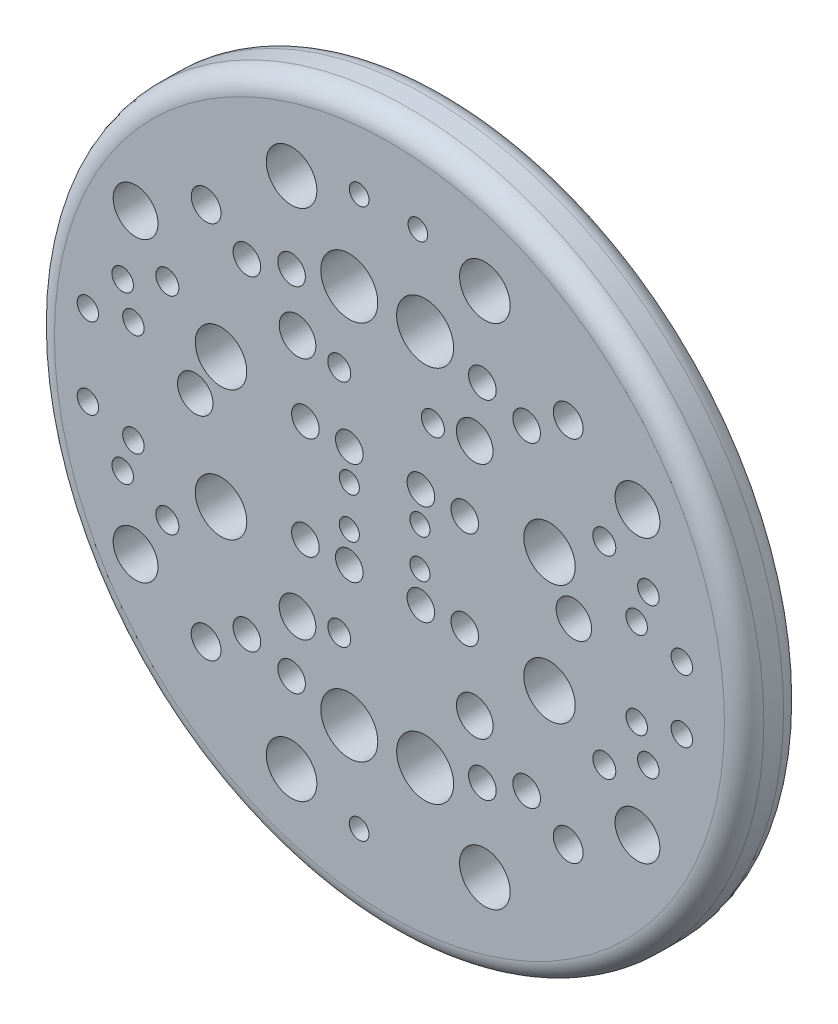
SolidWorks part; units mm, degrees
ref_plane "Front Plane" through (0, 0, 0) normal (0, 0, 1) x (1, 0, 0)
ref_plane "Top Plane" through (0, 0, 0) normal (0, 1, 0) x (1, 0, 0)
ref_plane "Right Plane" through (0, 0, 0) normal (1, 0, 0) x (0, 0, -1)
sketch "Sketch1" plane through (0, 0, 0) normal (0, 0, 1) x (1, 0, 0)
  circle A0 centre (0, 0) radius 9
  dimension "D1" = 18
extrude "Boss-Extrude1" add sketch "Sketch1" along normal blind 1.5
fillet "Fillet1" radius 0.5 2 edges at (9, 0, 0) (9, 0, 1.5)
sketch "Sketch2" plane through (0, 0, 0) normal (0, 0, -1) x (-1, 0, 0)
  line L0 (0, 8.5) -> (0.2605, -8.496) construction
  line L1 (-8.5, 0) -> (8.5, 0) construction
  circle A0 centre (0, 0) radius 8.5 construction
  circle A1 centre (0.7689, 6.9703) radius 0.2496
  circle A2 centre (2.4831, 6.5166) radius 0.6417
  circle A3 centre (3.6175, 4.1217) radius 0.3502
  circle A4 centre (4.6511, 4.8023) radius 0.3781
  circle A5 centre (2.4831, 4.4719) radius 0.3502
  circle A6 centre (2.3318, 3.0881) radius 0.4648
  circle A7 centre (2.1329, 1.2983) radius 0.3502
  circle A8 centre (4.273, 1.6485) radius 0.6537
  circle A9 centre (5.6343, 2.6233) radius 0.2915
  circle A10 centre (6.4409, 3.7715) radius 0.5688
  circle A11 centre (6.7687, 2.105) radius 0.2727
  circle A12 centre (6.496, 1.2983) radius 0.2727
  circle A13 centre (7.651, 1.0256) radius 0.2715
  circle A14 centre (4.9267, 0.5168) radius 0.4499
  circle A15 centre (1.0184, 4.8221) radius 0.7229
  circle A16 centre (1.2731, 2.9148) radius 0.2915
  circle A17 centre (1.0184, 1.2983) radius 0.3502
  circle A18 centre (1.0184, 0.5168) radius 0.2546
  circle A19 centre (-0.7733, 0.4893) radius 0.2546
  circle A20 centre (-0.7973, 1.2704) radius 0.3502
  circle A21 centre (-1.9112, 1.2363) radius 0.3502
  circle A22 centre (-1.1013, 2.8784) radius 0.2915
  circle A23 centre (-2.1649, 3.0192) radius 0.4648
  circle A24 centre (-4.6798, 0.3696) radius 0.4499
  circle A25 centre (-4.061, 1.5208) radius 0.6537
  circle A26 centre (-5.4515, 2.4534) radius 0.2915
  circle A27 centre (-6.2723, 1.1026) radius 0.2727
  circle A28 centre (-7.4184, 0.7947) radius 0.2715
  circle A29 centre (-6.5695, 1.9006) radius 0.2727
  circle A30 centre (-6.293, 3.5763) radius 0.5688
  circle A31 centre (-4.5356, 4.6616) radius 0.3781
  circle A32 centre (-3.4817, 4.0129) radius 0.3502
  circle A33 centre (-2.3585, 4.3977) radius 0.3502
  circle A34 centre (-2.4212, 6.4414) radius 0.6417
  circle A35 centre (-0.7216, 6.9475) radius 0.2496
  circle A36 centre (-0.9053, 4.7927) radius 0.7229
  circle A37 centre (7.651, -1.0256) radius 0.2715
  circle A38 centre (6.7687, -2.105) radius 0.2727
  circle A39 centre (6.496, -1.2983) radius 0.2727
  circle A40 centre (6.4409, -3.7715) radius 0.5688
  circle A41 centre (5.6343, -2.6233) radius 0.2915
  circle A42 centre (4.273, -1.6485) radius 0.6537
  circle A43 centre (2.1329, -1.2983) radius 0.3502
  circle A44 centre (2.3318, -3.0881) radius 0.4648
  circle A45 centre (2.4831, -4.4719) radius 0.3502
  circle A46 centre (3.6175, -4.1217) radius 0.3502
  circle A47 centre (4.6511, -4.8023) radius 0.3781
  circle A48 centre (0.7689, -6.9703) radius 0.2496
  circle A49 centre (2.4831, -6.5166) radius 0.6417
  circle A50 centre (1.0184, -4.8221) radius 0.7229
  circle A51 centre (1.2731, -2.9148) radius 0.2915
  circle A52 centre (1.0184, -1.2983) radius 0.3502
  circle A53 centre (1.0184, -0.5168) radius 0.2546
  circle A54 centre (-0.7973, -1.2704) radius 0.3502
  circle A55 centre (-0.7733, -0.4893) radius 0.2546
  circle A56 centre (-1.9112, -1.2363) radius 0.3502
  circle A57 centre (-2.3585, -4.3977) radius 0.3502
  circle A58 centre (-0.9053, -4.7927) radius 0.7229
  circle A59 centre (-3.4817, -4.0129) radius 0.3502
  circle A60 centre (-2.1649, -3.0192) radius 0.4648
  circle A61 centre (-4.061, -1.5208) radius 0.6537
  circle A62 centre (-5.4515, -2.4534) radius 0.2915
  circle A63 centre (-6.2723, -1.1026) radius 0.2727
  circle A64 centre (-7.4184, -0.7947) radius 0.2715
  circle A65 centre (-6.5695, -1.9006) radius 0.2727
  circle A66 centre (-6.293, -3.5763) radius 0.5688
  circle A67 centre (-4.5356, -4.6616) radius 0.3781
  circle A68 centre (-2.4212, -6.4414) radius 0.6417
extrude "Cut-Extrude1" cut sketch "Sketch2" against normal blind 1.5
